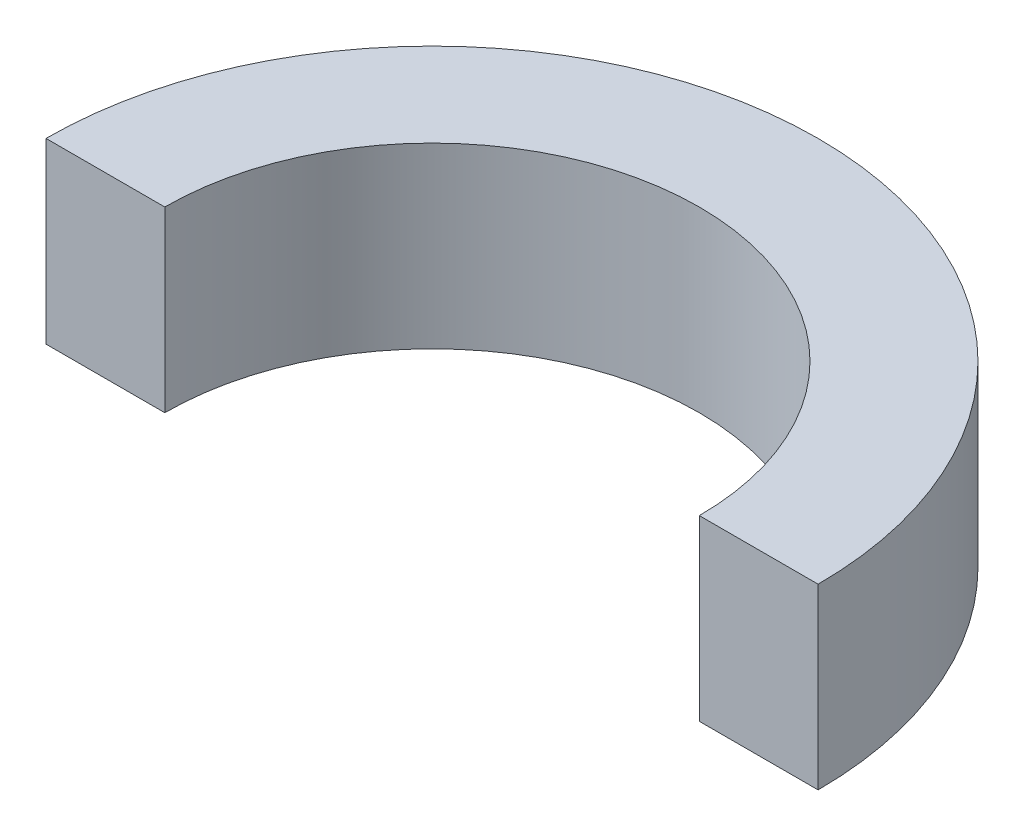
SolidWorks part; units mm, degrees
ref_plane "Front Plane" through (0, 0, 0) normal (0, 0, 1) x (1, 0, 0)
ref_plane "Top Plane" through (0, 0, 0) normal (0, 1, 0) x (1, 0, 0)
ref_plane "Right Plane" through (0, 0, 0) normal (1, 0, 0) x (0, 0, -1)
sketch "Sketch1" plane through (0, 0, 0) normal (0, 1, 0) x (1, 0, 0)
  line L0 (-13, 0) -> (-9, 0)
  line L1 (9, 0) -> (13, 0)
  circle A0 centre (0, 0) radius 12.43 construction
  circle A1 centre (0, 0) radius 9.43 construction
  circle A2 centre (0, 0) radius 13 construction
  circle A3 centre (0, 0) radius 9 construction
  arc A4 (9, 0) -> (-9, 0) centre (0, 0) ccw
  arc A5 (13, 0) -> (-13, 0) centre (0, 0) ccw
  dimension "D1" = 18.86
  dimension "D2" = 24.86
  dimension "D3" = 26
  dimension "D4" = 18
extrude "Boss-Extrude1" add sketch "Sketch1" along normal blind 6
